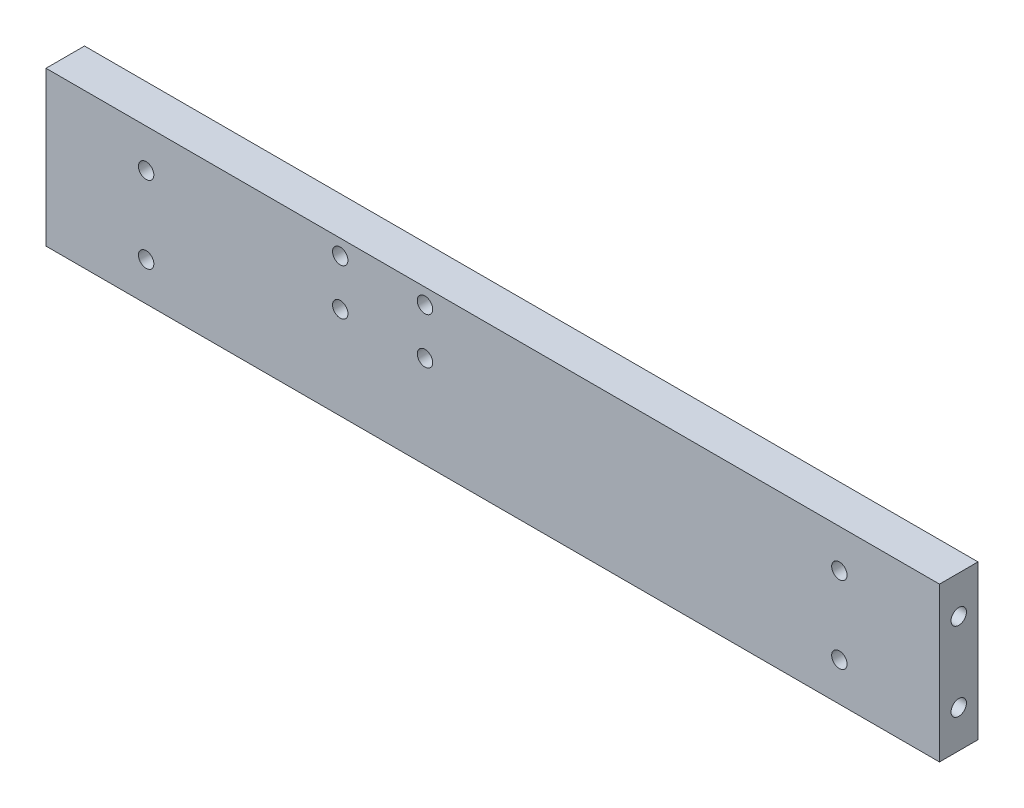
SolidWorks part; units mm, degrees
ref_plane "Front Plane" through (0, 0, 0) normal (0, 0, 1) x (1, 0, 0)
ref_plane "Top Plane" through (0, 0, 0) normal (0, 1, 0) x (1, 0, 0)
ref_plane "Right Plane" through (0, 0, 0) normal (1, 0, 0) x (0, 0, -1)
sketch "Sketch1" plane through (0, 0, 0) normal (0, 0, 1) x (1, 0, 0)
  line L1 (-58, 10) -> (58, 10)
  line L2 (-58, 10) -> (-58, -10)
  line L3 (-58, -10) -> (58, -10)
  line L4 (58, 10) -> (58, -10)
  line L5 (-58, 10) -> (58, -10) construction
  line L6 (-58, -10) -> (58, 10) construction
  line L11 (-15.5, 15.5) -> (15.5, -15.5) construction
  line L12 (-15.5, -15.5) -> (15.5, 15.5) construction
  point P0 (0, 0)
  dimension "D1" = 20
  dimension "D2" = 116
  dimension "D4" = 31
  dimension "D5" = 31
extrude "Boss-Extrude2" add sketch "Sketch1" along normal blind 5
ref_plane "Plane1" through (58, 0, 0) normal (1, 0, 0) x (0, 0, -1)
sketch "Sketch4" plane through (58, 0, 0) normal (1, 0, 0) x (0, 0, -1)
  line L0 (-5, 0) -> (0, 0)
  line L1 (-5, 10) -> (-5, -10) construction
  line L2 (0, 11) -> (0, -11) construction
  circle A0 centre (-2.5, 5.12) radius 1
  circle A1 centre (-2.5, -5.12) radius 1
  dimension "D1" = 2
  dimension "D2" = 5.12
  dimension "D3" = 2.5
extrude "Cut-Extrude1" cut sketch "Sketch4" against normal blind 10 contours A1 | A0
ref_plane "Plane2" through (58, 0, 0) normal (1, 0, 0) x (0, 0, -1)
ref_plane "Plane3" through (-58, 0, 0) normal (-1, 0, 0) x (0, 0, 1)
sketch "Sketch6" plane through (-58, 0, 0) normal (-1, 0, 0) x (0, 0, 1)
  line L0 (0, 0) -> (5, 0)
  line L1 (0, 10) -> (0, -10) construction
  line L2 (5, 10) -> (5, -10) construction
  circle A0 centre (2.5, 5) radius 1
  circle A1 centre (2.5, -5) radius 1
  dimension "D2" = 2
  dimension "D1" = 5
  dimension "D3" = 2.5
extrude "Cut-Extrude2" cut sketch "Sketch6" against normal blind 5 contours A0 | A1
ref_plane "Plane4" through (0, 0, 0) normal (0, 0, -1) x (-1, 0, 0)
sketch "Sketch7" plane through (0, 0, 0) normal (0, 0, -1) x (-1, 0, 0)
  line L0 (58, 10) -> (-58, 10) construction
  line L1 (50, -10) -> (-50, -10)
  line L2 (50, -10) -> (50, 10)
  line L3 (50, 10) -> (-50, 10)
  line L4 (-50, -10) -> (-50, 10)
  line L5 (50, -10) -> (-50, 10) construction
  line L6 (50, 10) -> (-50, -10) construction
  line L7 (-50, 0) -> (50, 0)
  line L8 (0, 10) -> (0, -10)
  circle A0 centre (-45, 5) radius 1
  circle A1 centre (-45, -5) radius 1
  circle A2 centre (45, 5) radius 1
  circle A3 centre (45, -5) radius 1
  point P0 (0, 0)
  dimension "D2" = 2
  dimension "D3" = 5
  dimension "D4" = 5
  dimension "D1" = 100
extrude "Cut-Extrude3" cut sketch "Sketch7" against normal through all contours A0 | A1 | A3 | A2
ref_plane "Plane5" through (0, 0, 0) normal (0, 0, -1) x (-1, 0, 0)
sketch "Sketch8" plane through (0, 0, 0) normal (0, 0, -1) x (-1, 0, 0)
  line L0 (58, 10) -> (-58, 10) construction
  line L1 (6.8, 10) -> (21.8, 10)
  line L2 (6.8, 10) -> (6.8, 0)
  line L3 (6.8, 0) -> (21.8, 0)
  line L4 (21.8, 10) -> (21.8, 0)
  line L5 (2.75, 0) -> (-2.75, 0) construction
  line L6 (58, -2.75) -> (58, 2.75) construction
  line L7 (14.3, 10) -> (14.3, 0)
  line L8 (14.3, 0) -> (6.8, 5)
  line L9 (6.8, 5) -> (21.8, 5)
  circle A0 centre (19.8, 8) radius 1
  circle A1 centre (8.8, 8) radius 1
  circle A2 centre (8.8, 2) radius 1
  circle A3 centre (19.8, 2) radius 1
  dimension "D3" = 2
  dimension "D4" = 2
  dimension "D5" = 2
  dimension "D1" = 36.2
  dimension "D2" = 15
extrude "Cut-Extrude4" cut sketch "Sketch8" against normal through all contours A1 | A2 | A3 | A0
